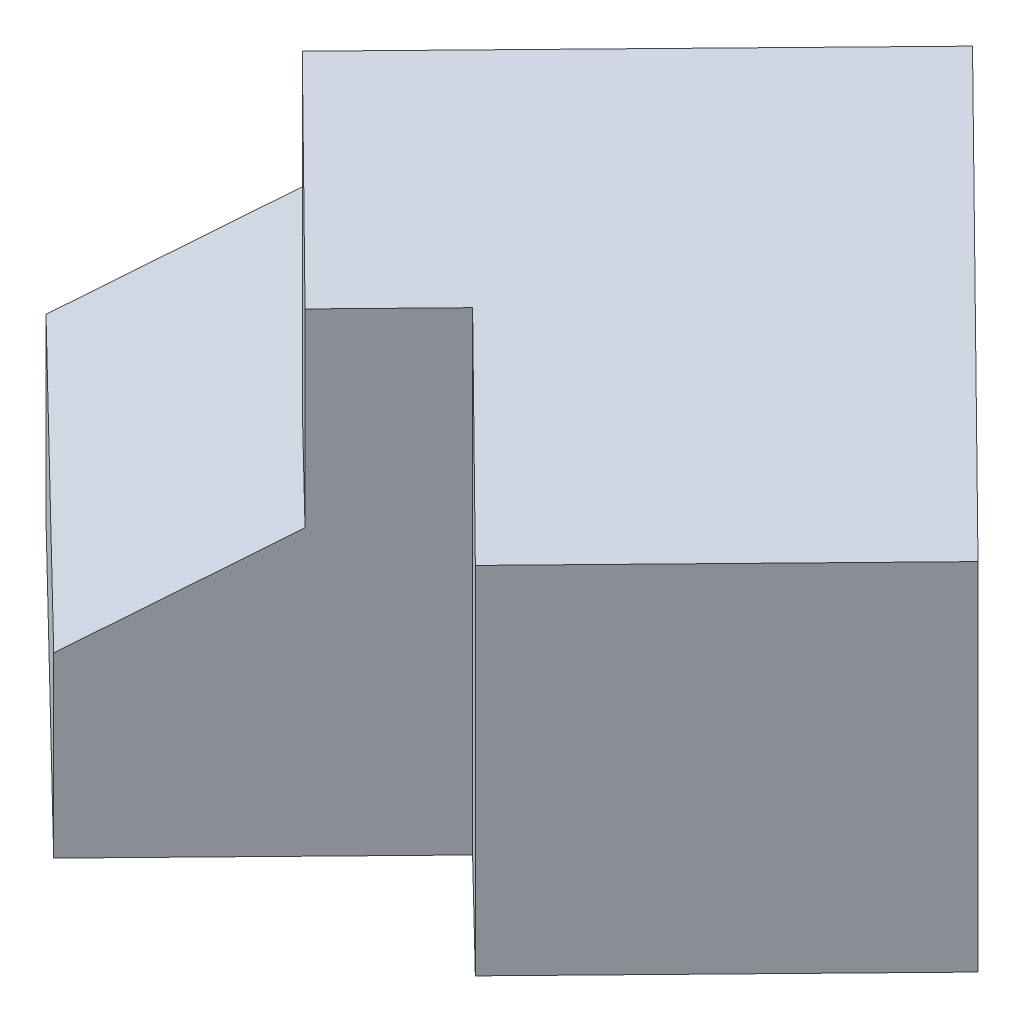
SolidWorks part; units mm, degrees
other "Perspective"
ref_plane "Front Plane" through (0, 0, 0) normal (0, 0, 1) x (1, 0, 0)
ref_plane "Top Plane" through (0, 0, 0) normal (0, 1, 0) x (1, 0, 0)
ref_plane "Right Plane" through (0, 0, 0) normal (1, 0, 0) x (0, 0, -1)
sketch "Sketch1" plane through (0, 0, 0) normal (0, 1, 0) x (1, 0, 0)
  line L0 (0, 0) -> (-50.1432, 48.8432)
  line L1 (-50.1432, 48.8432) -> (-15.2552, 84.6598)
  line L2 (-15.2552, 84.6598) -> (34.888, 35.8166)
  line L3 (34.888, 35.8166) -> (0, 0)
  dimension "D1" = 70
  dimension "D2" = 50
extrude "Extrude1" add sketch "Sketch1" along normal blind 60
sketch "Sketch2" plane through (0, 0, 0) normal (0.7163, 0, 0.6978) x (0.6978, 0, -0.7163)
  line L0 (50, 60) -> (0, 30)
  line L1 (0, 60) -> (0, 0) construction
  line L2 (0, 30) -> (0, 60)
  line L3 (0, 60) -> (50, 60)
  dimension "D1" = 30
extrude "Extrude2" cut sketch "Sketch2" against normal through all
sketch "Sketch3" plane through (0, 0, 0) normal (0, 1, 0) x (1, 0, 0)
  line L0 (20.9328, 21.4899) -> (3.0245, 38.9339)
  line L1 (0, 0) -> (34.888, 35.8166) construction
  line L2 (3.0245, 38.9339) -> (58.8453, 96.2405)
  line L3 (58.8453, 96.2405) -> (94.6619, 61.3525)
  line L4 (94.6619, 61.3525) -> (52.7963, 18.3726)
  line L5 (52.7963, 18.3726) -> (34.888, 35.8166)
  line L6 (34.888, 35.8166) -> (20.9328, 21.4899)
  line L7 (34.888, 35.8166) -> (-15.2552, 84.6598) construction
  dimension "D1" = 50
  dimension "D2" = 25
  dimension "D3" = 60
  dimension "D4" = 20
extrude "Extrude3" add sketch "Sketch3" along normal blind 100
sketch "Sketch4" plane through (20.9328, 0, -21.4899) normal (-0.6978, 0, 0.7163) x (0.7163, 0, 0.6978)
  line L0 (25, 60) -> (-25, 100)
  line L1 (25, 100) -> (25, 0) construction
  line L2 (-25, 100) -> (25, 100)
  line L3 (25, 100) -> (25, 60)
  dimension "D1" = 40
extrude "Extrude4" cut sketch "Sketch4" against normal blind 100
